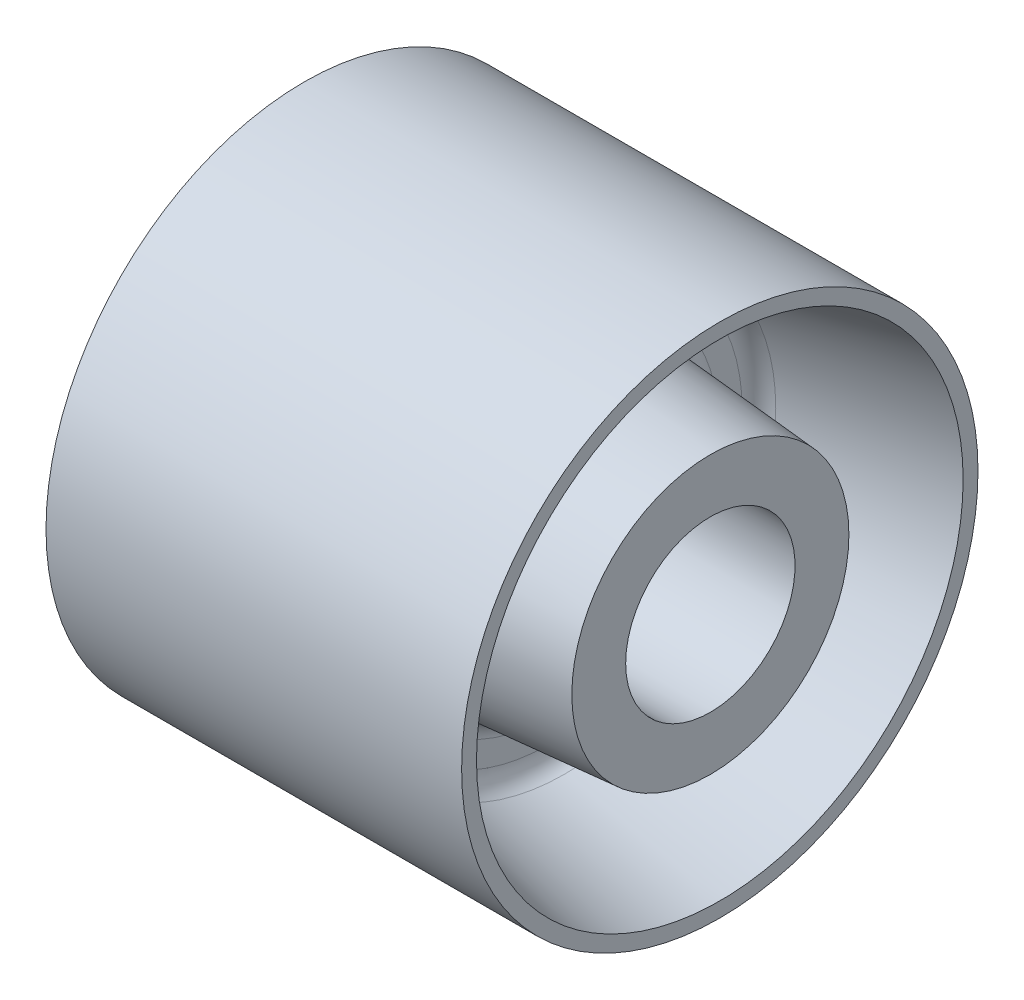
SolidWorks part; units mm, degrees
material "Gray Cast Iron"
ref_plane "Front" through (0, 0, 0) normal (0, 0, 1) x (1, 0, 0)
ref_plane "Top" through (0, 0, 0) normal (0, 1, 0) x (1, 0, 0)
ref_plane "Right" through (0, 0, 0) normal (1, 0, 0) x (0, 0, -1)
sketch "Sketch1" plane through (0, 0, 0) normal (0, 0, 1) x (1, 0, 0)
  line L0 (0, 81.9524) -> (0, -101.7282) construction
  line L1 (-113.6273, 0) -> (105.918, 0) construction
  line L2 (0, 13.45) -> (0, 41)
  line L3 (0, 41) -> (33, 41)
  line L4 (33, 41) -> (33, 38.64)
  line L5 (33, 38.64) -> (6, 33)
  line L6 (6, 33) -> (6, 24)
  line L7 (6, 24) -> (31.5, 22)
  line L8 (31.5, 22) -> (31.5, 13.45)
  line L9 (31.5, 13.45) -> (0, 13.45)
  dimension "D1" = 12
  dimension "D2" = 66
  dimension "D3" = 63
  dimension "D4" = 82
  dimension "D5" = 77.28
  dimension "D6" = 66
  dimension "D7" = 48
  dimension "D8" = 44
  dimension "D9" = 26.9
revolve "Revolve1" add sketch "Sketch1" angle 360 about L1
fillet "Fillet4" radius 3 1 edges at (6, 0, 33)
fillet "Fillet5" radius 3 1 edges at (6, 0, 24)
mirror "Mirror1" about plane through (0, 0, 0) normal (1, 0, 0) of bodies 101
